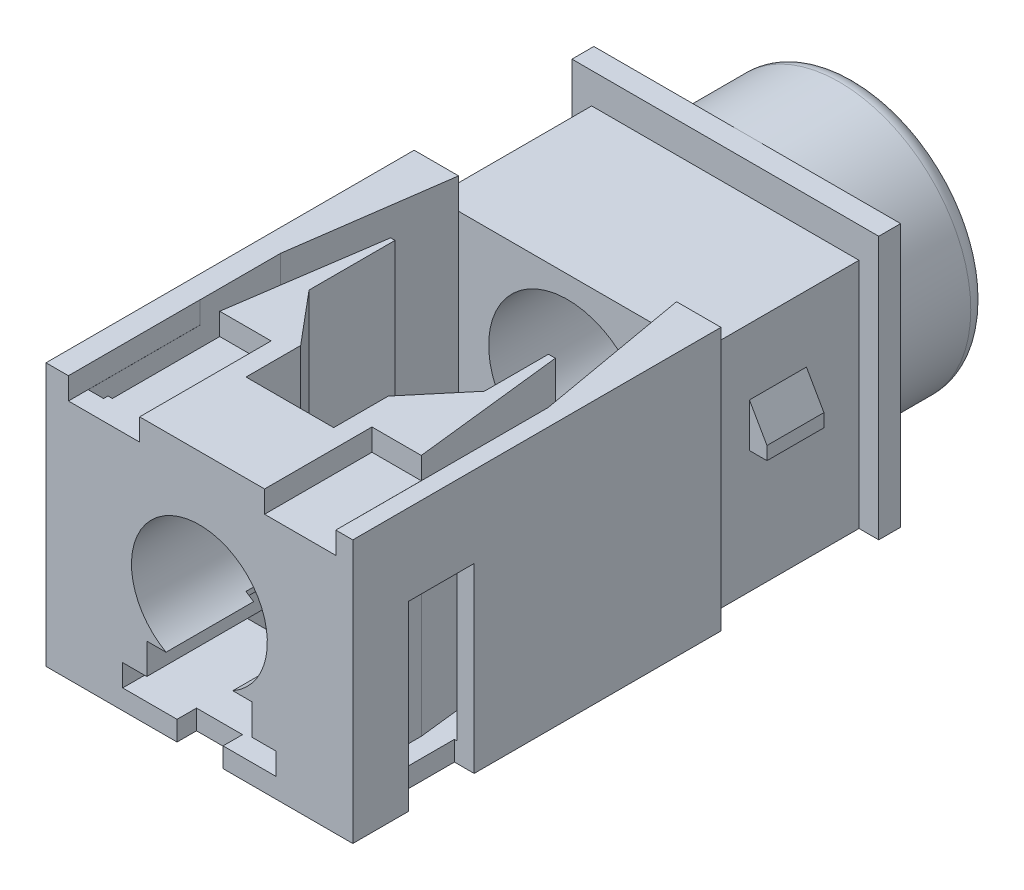
SolidWorks part; units mm, degrees
ref_plane "Front Plane" through (0, 0, 0) normal (0, 0, 1) x (1, 0, 0)
ref_plane "Top Plane" through (0, 0, 0) normal (0, 1, 0) x (1, 0, 0)
ref_plane "Right Plane" through (0, 0, 0) normal (1, 0, 0) x (0, 0, -1)
sketch "Szkic1" plane through (0, 0, 0) normal (0, 0, 1) x (1, 0, 0)
  circle A0 centre (0, 0) radius 3
  circle A1 centre (0, 0) radius 1.8
  dimension "D1" = 6
  dimension "D2" = 3.6
extrude "Dodanie-wyciągnięcie1" add sketch "Szkic1" along normal blind 2.5
sketch "Szkic2" plane through (0, 0, 2.5) normal (0, 0, 1) x (1, 0, 0)
  line L5 (3.5, -3) -> (-3.5, -3)
  line L6 (3.5, -3) -> (3.5, 3)
  line L7 (3.5, 3) -> (-3.5, 3)
  line L8 (-3.5, -3) -> (-3.5, 3)
  line L9 (3.5, -3) -> (-3.5, 3) construction
  line L10 (3.5, 3) -> (-3.5, -3) construction
  circle A2 centre (0, 0) radius 1.8 construction
  circle A3 centre (0, 0) radius 1.8
  dimension "D1" = 6
  dimension "D2" = 7
extrude "Dodanie-wyciągnięcie2" add sketch "Szkic2" along normal blind 0.5
fillet "Zaokrąglenie1" radius 0.4 1 edges at (3, 0, 0)
chamfer "Sfazowanie1" distance 0.4 angle 45 1 edges at (1.8, 0, 0)
sketch "Szkic3" plane through (0, 0, 3) normal (0, 0, 1) x (1, 0, 0)
  line L0 (0, 2.3) -> (0, -3) construction
  line L1 (-3.5, -3) -> (3.5, -3) construction
  line L2 (-3.05, 2.3) -> (3.05, 2.3)
  line L3 (-3.05, 2.3) -> (-3.05, -3)
  line L4 (-3.05, -3) -> (3.05, -3)
  line L5 (3.05, -3) -> (3.05, 2.3)
  line L6 (3.5, 3) -> (-3.5, 3) construction
  circle A0 centre (0, 0) radius 1.8 construction
  circle A1 centre (0, 0) radius 1.8
  dimension "D1" = 0.7
  dimension "D2" = 6.1
extrude "Dodanie-wyciągnięcie3" add sketch "Szkic3" along normal blind 3.6
ref_plane "Płaszczyzna1" through (0, 0, 4.3) normal (0, 0, 1) x (1, 0, 0)
sketch "Szkic4" plane through (0, 0, 4.3) normal (0, 0, 1) x (1, 0, 0)
  line L0 (3.05, 0.7904) -> (3.05, 3) construction
  line L1 (3.05, 3) -> (3.5, 3) construction
  line L2 (3.05, 0.7904) -> (3.05, -0.2096)
  line L3 (3.05, -0.2096) -> (3.45, -0.2096)
  line L4 (3.45, -0.2096) -> (3.45, 0.0904)
  line L5 (3.45, 0.0904) -> (3.05, 0.7904)
extrude "Dodanie-wyciągnięcie4" add sketch "Szkic4" along normal blind 1.3 from offset 0.1 separate body offset against normal yes
mirror "Lustro1" about plane through (0, 0, 0) normal (1, 0, 0) of bodies 104
sketch "Szkic5" plane through (0, 0, 6.6) normal (0, 0, 1) x (1, 0, 0)
  line L0 (-3.5, -3) -> (3.5, -3)
  line L1 (-3.5, -3) -> (-3.5, 3)
  line L2 (-3.5, 3) -> (-3.5, -3) construction
  line L3 (-3.5, 3) -> (3.5, 3)
  line L4 (3.5, 3) -> (3.5, -3)
  circle A0 centre (0, 0) radius 1.55
  dimension "D2" = 3.1
  dimension "D1" = 6
extrude "Dodanie-wyciągnięcie5" add sketch "Szkic5" along normal blind 8.4 separate body
sketch "Szkic7" plane through (0, -3, 0) normal (0, -1, 0) x (1, 0, 0)
  line L0 (1.75, 11.0559) -> (1.75, 12.2059)
  line L1 (0.9, 11.0559) -> (1.75, 11.0559)
  line L2 (0.9, 12.2059) -> (0.9, 11.0559)
  line L3 (1.75, 12.2059) -> (0.9, 12.2059)
  line L4 (-1.75, 11.0559) -> (-0.9, 11.0559)
  line L5 (-1.75, 12.2059) -> (-1.75, 11.0559)
  line L6 (-0.9, 11.0559) -> (-0.9, 12.2059)
  line L7 (-0.9, 12.2059) -> (-1.75, 12.2059)
  line L8 (0.54, 14.5559) -> (0.54, 15.0309)
  line L9 (-0.51, 14.5559) -> (0.54, 14.5559)
  line L10 (-0.51, 15.0309) -> (-0.51, 14.5559)
  line L11 (3.05, 12.2309) -> (3.05, 13.5309)
  line L12 (3.5, 12.2309) -> (3.05, 12.2309)
  line L13 (3.5, 12.2309) -> (3.5, 13.7309)
  line L14 (3.05, 13.7309) -> (3.5, 13.7309)
  line L15 (3.05, 13.7309) -> (3.05, 14.5809)
  line L16 (2.7, 14.5809) -> (3.05, 14.5809)
  line L17 (2.7, 14.5809) -> (2.7, 13.5309)
  line L18 (3.05, 13.5309) -> (2.7, 13.5309)
  line L19 (-3.05, 13.7309) -> (-3.5, 13.7309)
  line L20 (-3.5, 13.7309) -> (-3.5, 12.2309)
  line L21 (-3.05, 12.2309) -> (-3.5, 12.2309)
  line L22 (-3.05, 13.5309) -> (-3.05, 12.2309)
  line L23 (-2.7, 13.5309) -> (-3.05, 13.5309)
  line L24 (-3.05, 14.5809) -> (-3.05, 13.7309)
  line L25 (-3.05, 14.5809) -> (-2.7, 14.5809)
  line L26 (-2.7, 13.5309) -> (-2.7, 14.5809)
  line L27 (0.015, 15.0309) -> (0.0296, 18.44) construction
  line L28 (-0.51, 15.0309) -> (0.54, 15.0309)
  circle A0 centre (0, 4.5309) radius 0.475
  circle A1 centre (0, 11.5309) radius 0.475
sketch "Szkic8" plane through (0, -3, 0) normal (0, -1, 0) x (1, 0, 0)
  circle A0 centre (0, 11.5309) radius 0.475 construction
  circle A1 centre (0, 4.5309) radius 0.475 construction
  circle A2 centre (0, 11.5309) radius 0.475
  circle A3 centre (0, 4.5309) radius 0.475
extrude "Dodanie-wyciągnięcie6" add sketch "Szkic8" along normal blind 0.8 separate body
fillet "Zaokrąglenie2" radius 0.2 1 edges at (0.475, -3.8, 4.5309)
fillet "Zaokrąglenie3" radius 0.2 1 edges at (0.475, -3.8, 11.5309)
sketch "Szkic9" plane through (0, -3, 0) normal (0, -1, 0) x (1, 0, 0)
  line L0 (0.9, 11.0559) -> (1.75, 11.0559) construction
  line L1 (1.75, 11.0559) -> (1.75, 12.2059) construction
  line L2 (1.75, 12.2059) -> (0.9, 12.2059) construction
  line L3 (0.9, 12.2059) -> (0.9, 11.0559) construction
  line L4 (-0.9, 12.2059) -> (-1.75, 12.2059) construction
  line L5 (-1.75, 12.2059) -> (-1.75, 11.0559) construction
  line L6 (-1.75, 11.0559) -> (-0.9, 11.0559) construction
  line L7 (-0.9, 11.0559) -> (-0.9, 12.2059) construction
  line L8 (0.9, 11.0559) -> (1.75, 11.0559)
  line L9 (1.75, 11.0559) -> (1.75, 12.2059)
  line L10 (1.75, 12.2059) -> (0.9, 12.2059)
  line L11 (0.9, 12.2059) -> (0.9, 11.0559)
  line L12 (-0.9, 12.2059) -> (-1.75, 12.2059)
  line L13 (-1.75, 12.2059) -> (-1.75, 11.0559)
  line L14 (-1.75, 11.0559) -> (-0.9, 11.0559)
  line L15 (-0.9, 11.0559) -> (-0.9, 12.2059)
extrude "Wytnij-wyciągnięcie1" cut sketch "Szkic9" against normal blind 0.95
sketch "Szkic10" plane through (0, -3, 0) normal (0, -1, 0) x (1, 0, 0)
  line L0 (0.54, 14.5559) -> (0.54, 15.0309) construction
  line L1 (-0.51, 14.5559) -> (0.54, 14.5559) construction
  line L2 (-0.51, 15.0309) -> (-0.51, 14.5559) construction
  line L3 (-0.51, 15.0309) -> (0.54, 15.0309) construction
  line L4 (0.54, 14.5559) -> (0.54, 15.0309)
  line L5 (-0.51, 14.5559) -> (0.54, 14.5559)
  line L6 (-0.51, 15.0309) -> (-0.51, 14.5559)
  line L7 (-0.51, 15.0309) -> (0.54, 15.0309)
extrude "Wytnij-wyciągnięcie2" cut sketch "Szkic10" against normal blind 2
sketch "Szkic11" plane through (0, -3, 0) normal (0, -1, 0) x (1, 0, 0)
  line L0 (3.05, 13.5309) -> (2.7, 13.5309) construction
  line L1 (2.7, 14.5809) -> (2.7, 13.5309) construction
  line L2 (2.7, 14.5809) -> (3.05, 14.5809) construction
  line L3 (3.05, 13.7309) -> (3.05, 14.5809) construction
  line L4 (3.05, 13.7309) -> (3.5, 13.7309) construction
  line L5 (3.5, 12.2309) -> (3.5, 13.7309) construction
  line L6 (3.5, 12.2309) -> (3.05, 12.2309) construction
  line L7 (3.05, 12.2309) -> (3.05, 13.5309) construction
  line L8 (-3.05, 13.5309) -> (-3.05, 12.2309) construction
  line L9 (-2.7, 13.5309) -> (-3.05, 13.5309) construction
  line L10 (-2.7, 13.5309) -> (-2.7, 14.5809) construction
  line L11 (-3.05, 14.5809) -> (-2.7, 14.5809) construction
  line L12 (-3.05, 14.5809) -> (-3.05, 13.7309) construction
  line L13 (-3.05, 13.7309) -> (-3.5, 13.7309) construction
  line L14 (-3.5, 13.7309) -> (-3.5, 12.2309) construction
  line L15 (-3.05, 12.2309) -> (-3.5, 12.2309) construction
  line L16 (3.05, 13.5309) -> (2.7, 13.5309)
  line L17 (2.7, 14.5809) -> (2.7, 13.5309)
  line L18 (2.7, 14.5809) -> (3.05, 14.5809)
  line L19 (3.05, 13.7309) -> (3.05, 14.5809)
  line L20 (3.05, 13.7309) -> (3.5, 13.7309)
  line L21 (3.5, 12.2309) -> (3.5, 13.7309)
  line L22 (3.5, 12.2309) -> (3.05, 12.2309)
  line L23 (3.05, 12.2309) -> (3.05, 13.5309)
  line L24 (-3.05, 13.5309) -> (-3.05, 12.2309)
  line L25 (-2.7, 13.5309) -> (-3.05, 13.5309)
  line L26 (-2.7, 13.5309) -> (-2.7, 14.5809)
  line L27 (-3.05, 14.5809) -> (-2.7, 14.5809)
  line L28 (-3.05, 14.5809) -> (-3.05, 13.7309)
  line L29 (-3.05, 13.7309) -> (-3.5, 13.7309)
  line L30 (-3.5, 13.7309) -> (-3.5, 12.2309)
  line L31 (-3.05, 12.2309) -> (-3.5, 12.2309)
extrude "Wytnij-wyciągnięcie3" cut sketch "Szkic11" against normal blind 4.15
sketch "Szkic12" plane through (0, 0, 15) normal (0, 0, 1) x (1, 0, 0)
  line L0 (1.75, -2.05) -> (1.75, -2.55)
  line L1 (-1.75, -2.55) -> (-1.75, -2.05)
  line L2 (1.75, -2.55) -> (0.54, -2.55)
  line L3 (-0.51, -2.55) -> (-1.75, -2.55)
  line L4 (-1.2, -2.05) -> (-1.75, -2.05)
  line L5 (1.75, -2.05) -> (1.2, -2.05)
  line L6 (1.2, -1.35) -> (1.2, -2.05)
  line L7 (1.2, -1.35) -> (0.7616, -1.35)
  line L8 (-0.7616, -1.35) -> (-1.2, -1.35)
  line L9 (-1.2, -2.05) -> (-1.2, -1.35)
  line L10 (0, 1.55) -> (0, 3) construction
  line L11 (0.54, -2.55) -> (-0.51, -2.55)
  arc A0 (0.7616, -1.35) -> (-0.7616, -1.35) centre (0, 0) ccw
extrude "Wytnij-wyciągnięcie4" cut sketch "Szkic12" against normal up to surface (8.4 mm away) up to face at (0, 0, 6.6)
sketch "Szkic13" plane through (0, 3, 0) normal (0, 1, 0) x (1, 0, 0)
  line L0 (-2.9863, -10.1577) -> (-2.9863, -14.55)
  line L1 (-2.4863, -6.6) -> (-2.9863, -10.1577)
  line L2 (-2.4863, -6.6) -> (2.4863, -6.6)
  line L3 (3.1137, -14.55) -> (3.1137, -10.1577)
  line L4 (2.4863, -6.6) -> (3.1137, -10.1577)
  line L5 (-2.5363, -14.45) -> (-2.5363, -12)
  line L6 (-2.5363, -12) -> (-1.3613, -12)
  line L7 (-1.3613, -12) -> (-1.3613, -15)
  line L8 (-1.3613, -15) -> (1.4887, -15)
  line L9 (1.4887, -15) -> (1.4887, -12.55)
  line L10 (1.4887, -12.55) -> (2.6125, -12.55)
  line L11 (2.6125, -12.55) -> (2.2205, -9.1)
  line L12 (2.2205, -9.1) -> (2.0637, -9.1)
  line L13 (2.0637, -9.1) -> (2.0637, -10.5616)
  line L14 (2.0637, -10.5616) -> (1.0637, -11.7534)
  line L15 (1.0637, -11.7534) -> (1.0637, -13)
  line L16 (1.0637, -13) -> (-0.9363, -13)
  line L17 (-0.9363, -13) -> (-0.9363, -11.7534)
  line L18 (-0.9363, -11.7534) -> (-1.9363, -10.5616)
  line L19 (-1.9363, -10.5616) -> (-1.9363, -8.6)
  line L20 (-1.9363, -8.6) -> (-2.0363, -8.6)
  line L21 (-2.0363, -8.6) -> (-2.5363, -12)
  line L22 (-2.6363, -14.45) -> (-2.5363, -14.45)
  line L23 (-2.6363, -14.45) -> (-2.6363, -14.55)
  line L24 (-2.9863, -14.55) -> (-2.6363, -14.55)
  line L25 (2.6125, -12.55) -> (2.6125, -14.45)
  line L26 (2.6125, -14.45) -> (2.7637, -14.45)
  line L27 (2.7637, -14.45) -> (2.7637, -14.55)
  line L28 (3.1137, -14.55) -> (2.7637, -14.55)
  line L29 (0, -6.6) -> (0, -0.9682) construction
  line M17 (3.5, -6.6) -> (-3.5, -6.6)
extrude "Wytnij-wyciągnięcie5" cut sketch "Szkic13" against normal up to surface (5.55 mm away) contours L28 L3 L4 L2 L1 L0 L24 L23 L22 L5 L21 L20 L19 L18 L17 L16 L15 L14 L13 L12 L11 L25 L26 L27 M17 up to face at (0.0038, -2.55, 12.21)
sketch "Szkic14" plane through (0, 3, 0) normal (0, 1, 0) x (1, 0, 0)
  line L0 (0, -15) -> (0, -17.8683) construction
  line L1 (3.5, -15) -> (-3.5, -15) construction
  line L2 (3.1118, -15) -> (1.4868, -15)
  line L3 (1.4868, -15) -> (1.4868, -12.55)
  line L4 (1.4868, -12.55) -> (3.1118, -12.55)
  line L5 (3.1118, -12.55) -> (3.1118, -15)
  line L6 (-1.3632, -15) -> (-2.9882, -15)
  line L7 (-2.9882, -15) -> (-2.9882, -12)
  line L8 (-2.9882, -12) -> (-1.3632, -12)
  line L9 (-1.3632, -12) -> (-1.3632, -15)
  line L10 (-2.9882, -15) -> (-3.4382, -15) construction
extrude "Wytnij-wyciągnięcie6" cut sketch "Szkic14" against normal blind 0.5
